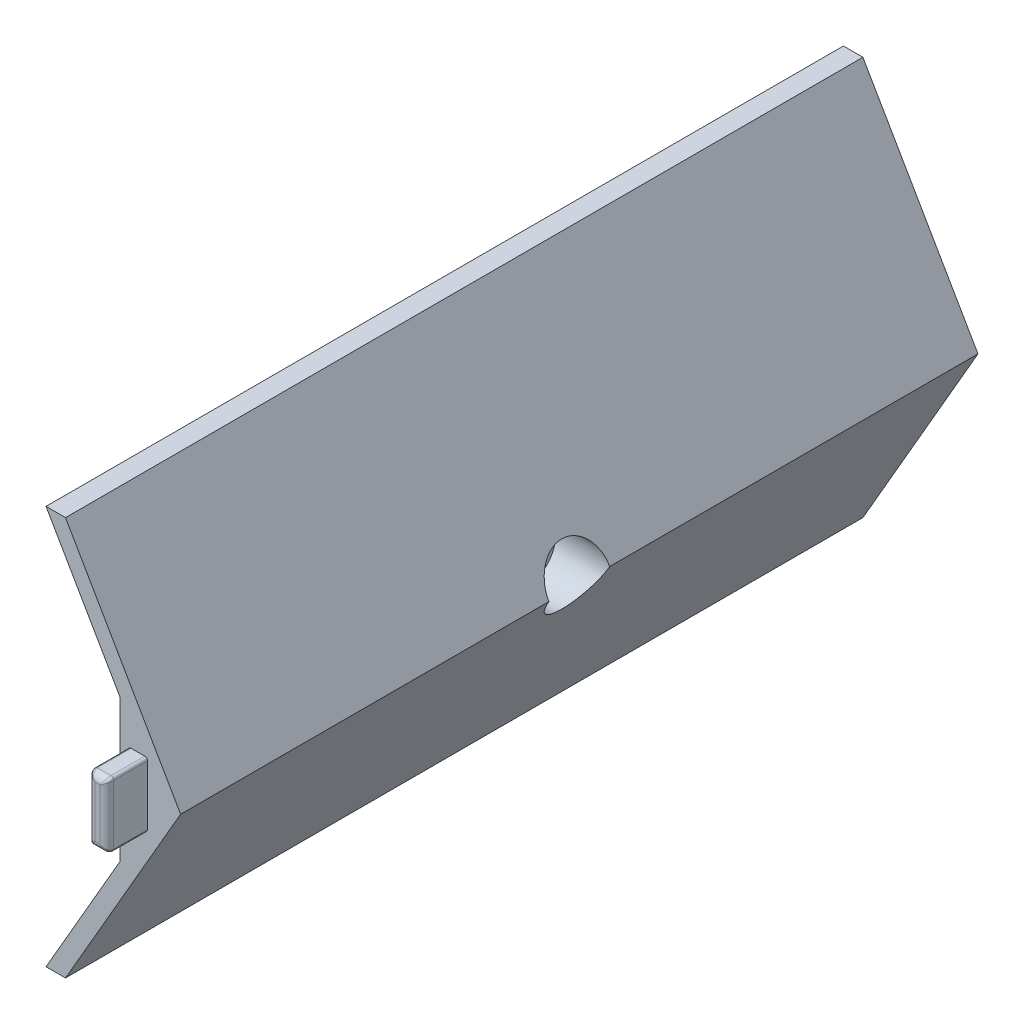
SolidWorks part; units mm, degrees
ref_plane "Front" through (0, 0, 0) normal (0, 0, 1) x (1, 0, 0)
ref_plane "Top" through (0, 0, 0) normal (0, 1, 0) x (1, 0, 0)
ref_plane "Right" through (0, 0, 0) normal (1, 0, 0) x (0, 0, -1)
sketch "Sketch1" plane through (0, 0, 0) normal (0, 0, 1) x (1, 0, 0)
  line L4 (17.5566, 0) -> (9.0407, 14.75)
  line L5 (10.4841, -14.75) -> (19, 0)
  line L6 (19, 0) -> (10.4841, 14.75)
  line L11 (19, 0) -> (3.3163, 0) construction
  line L13 (4.8053, -14.75) -> (4.8053, 14.75) construction
  line L15 (17.5566, 0) -> (9.0407, -14.75)
  line L20 (9.0407, -14.75) -> (10.4841, -14.75)
  line L21 (9.0407, 14.75) -> (10.4841, 14.75)
  point P4 (4.8053, 0)
  dimension "D2" = 1.4434
  dimension "D3" = 1.25
  dimension "D4" = 29.5
extrude "Boss-Extrude1" add sketch "Sketch1" along normal mid plane 59
sketch "Sketch2" plane through (0, 0, 29.5) normal (0, 0, 1) x (1, 0, 0)
  line L0 (17.5566, 0) -> (14.5, 5.2942)
  line L1 (9.0407, 14.75) -> (17.5566, 0) construction
  line L2 (14.5, 5.2942) -> (14.5, -5.2942)
  line L3 (17.5566, 0) -> (9.0407, -14.75) construction
  line L4 (14.5, -5.2942) -> (17.5566, 0)
  dimension "D1" = 4.5
extrude "Boss-Extrude2" add sketch "Sketch2" against normal blind 59
sketch "Sketch3" plane through (0, 0, 29.5) normal (0, 0, 1) x (1, 0, 0)
  line L0 (19, 0) -> (11.6776, 0) construction
  line L1 (14.5, 5.2942) -> (14.5, -5.2942) construction
  line L2 (16.55, 2.4) -> (15.15, 2.4)
  line L3 (16.55, 2.4) -> (16.55, -2.4)
  line L4 (16.55, -2.4) -> (15.15, -2.4)
  line L5 (15.15, 2.4) -> (15.15, -2.4)
  line L6 (16.55, 2.4) -> (15.15, -2.4) construction
  line L7 (16.55, -2.4) -> (15.15, 2.4) construction
  point P4 (15.85, 0)
  dimension "D1" = 1.4
  dimension "D2" = 4.8
  dimension "D3" = 4.8
  dimension "D4" = 0.65
extrude "Boss-Extrude3" add sketch "Sketch3" along normal blind 3
fillet "Fillet1" radius 0.5 4 edges at (15.85, 2.4, 32.5) (16.55, 0, 32.5) (15.85, -2.4, 32.5) (15.15, 0, 32.5)
ref_plane "Plane1" through (20, 0, 0) normal (1, 0, 0) x (0, 0, -1)
sketch "Sketch5" plane through (20, 0, 0) normal (1, 0, 0) x (0, 0, -1)
  circle A0 centre (0, 0) radius 1.2
  dimension "D1" = 2.4
extrude "Cut-Extrude1" cut sketch "Sketch5" against normal blind 13
sketch "Sketch6" plane through (20, 0, 0) normal (1, 0, 0) x (0, 0, -1)
  circle A0 centre (0, 0) radius 2.25
  dimension "D1" = 4.5
extrude "Cut-Extrude2" cut sketch "Sketch6" against normal blind 5
fillet "Fillet2" radius 0.2 8 edges at (15.2964, -2.2536, 32.3536) (15.2964, 2.2536, 32.3536) (16.4036, 2.2536, 32.3536) (16.4036, -2.2536, 32.3536) (15.15, -2.4, 30.75) (15.15, 2.4, 30.75) (16.55, 2.4, 30.75) (16.55, -2.4, 30.75)
